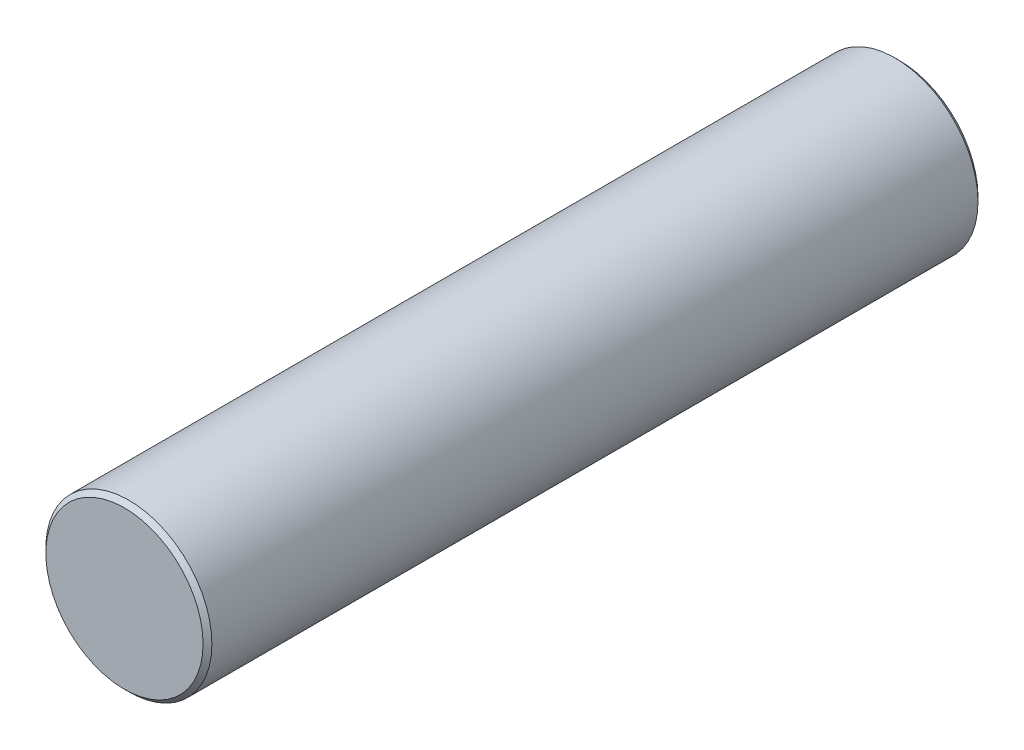
SolidWorks part; units mm, degrees
ref_plane "Front Plane" through (0, 0, 0) normal (0, 0, 1) x (1, 0, 0)
ref_plane "Top Plane" through (0, 0, 0) normal (0, 1, 0) x (1, 0, 0)
ref_plane "Right Plane" through (0, 0, 0) normal (1, 0, 0) x (0, 0, -1)
sketch "Sketch1" plane through (0, 0, 0) normal (0, 0, 1) x (1, 0, 0)
  circle A0 centre (0, 0) radius 2.3812
  dimension "D1" = 4.7625
extrude "Extrude1" add sketch "Sketch1" against normal blind 22.225
chamfer "Chamfer1" distance 0.127 angle 45 2 edges at (2.3812, 0, -22.225) (2.3812, 0, 0)
